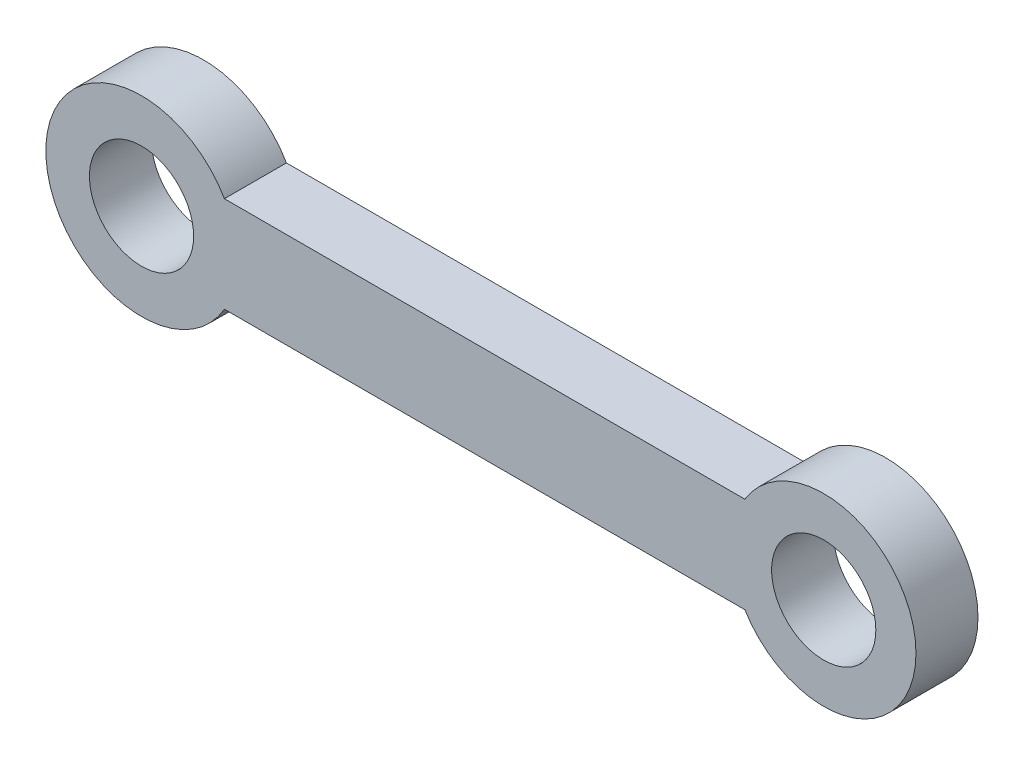
SolidWorks part; units mm, degrees
ref_plane "Front Plane" through (0, 0, 0) normal (0, 0, 1) x (1, 0, 0)
ref_plane "Top Plane" through (0, 0, 0) normal (0, 1, 0) x (1, 0, 0)
ref_plane "Right Plane" through (0, 0, 0) normal (1, 0, 0) x (0, 0, -1)
sketch "Sketch1" plane through (0, 0, 0) normal (0, 0, 1) x (1, 0, 0)
  line L0 (-63.4724, 0) -> (39.378, 0) construction
  line L1 (0, 8.4725) -> (0, -7.6636) construction
  line L2 (-27.5, 0) -> (-20.8178, 3.8579) construction
  line L3 (-20.8178, 3.8579) -> (21.1411, 3.8579)
  line L4 (-20.8178, -3.8579) -> (21.1411, -3.8579)
  arc A0 (-20.8178, 3.8579) -> (-20.8178, -3.8579) centre (-27.5, 0) ccw
  arc A1 (21.1411, -3.8579) -> (21.1411, 3.8579) centre (27.5, 0) ccw
  circle A2 centre (-27.5, 0) radius 4.2
  circle A3 centre (27.5, 0) radius 4.2
  dimension "D1" = 55
  dimension "D2" = 30
extrude "Boss-Extrude1" add sketch "Sketch1" along normal blind 5
